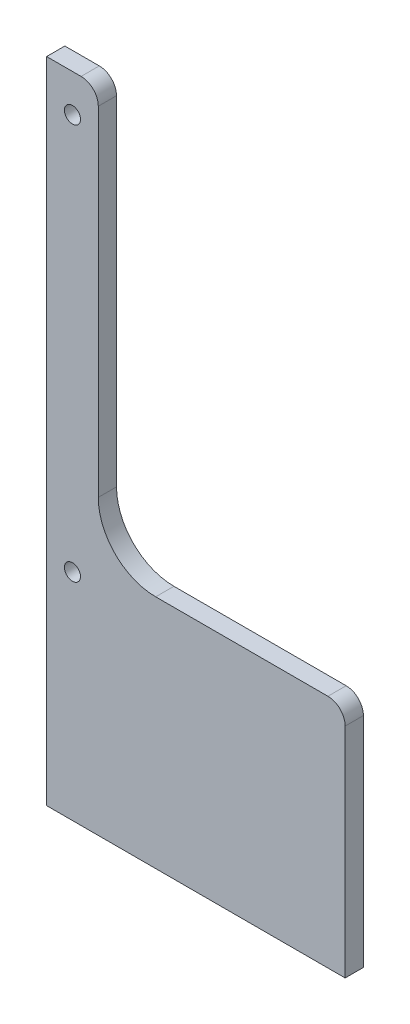
SolidWorks part; units mm, degrees
ref_plane "Front Plane" through (0, 0, 0) normal (0, 0, 1) x (1, 0, 0)
ref_plane "Top Plane" through (0, 0, 0) normal (0, 1, 0) x (1, 0, 0)
ref_plane "Right Plane" through (0, 0, 0) normal (1, 0, 0) x (0, 0, -1)
sketch "Sketch1" plane through (0, 0, 0) normal (0, 0, 1) x (1, 0, 0)
  line L0 (9, 81) -> (9, 9)
  line L1 (0, 0) -> (52, 0)
  line L2 (0, 0) -> (0, 81)
  line L3 (0, 81) -> (9, 81)
  line L4 (52, 0) -> (52, 83)
  line L5 (9, 9) -> (52, 9)
  line L6 (4.5, 81) -> (4.5, 0) construction
  line L8 (52, 0) -> (0, 0)
  line L9 (52, 0) -> (52, -32)
  line L10 (52, -32) -> (0, -32)
  line L11 (0, 0) -> (0, -32)
  circle A0 centre (4.5, 5.5) radius 1.4
  circle A1 centre (4.5, 74.47) radius 1.4
  dimension "D6" = 2.8
  dimension "D1" = 9
  dimension "D2" = 9
  dimension "D3" = 81
  dimension "D4" = 52
  dimension "D5" = 5.5
  dimension "D7" = 68.97
  dimension "D8" = 113
extrude "Boss-Extrude1" add sketch "Sketch1" along normal blind 3.175 contours L3 L6 A1 A0 L1 L4 L5 L0 | L6 L3 L2 L1 A0 A1 | L1 L11 L10 L9 L8
fillet "Fillet1" radius 10 1 edges at (9, 9, 1.5875)
fillet "Fillet2" radius 3 2 edges at (9, 81, 1.5875) (52, 9, 1.5875)
